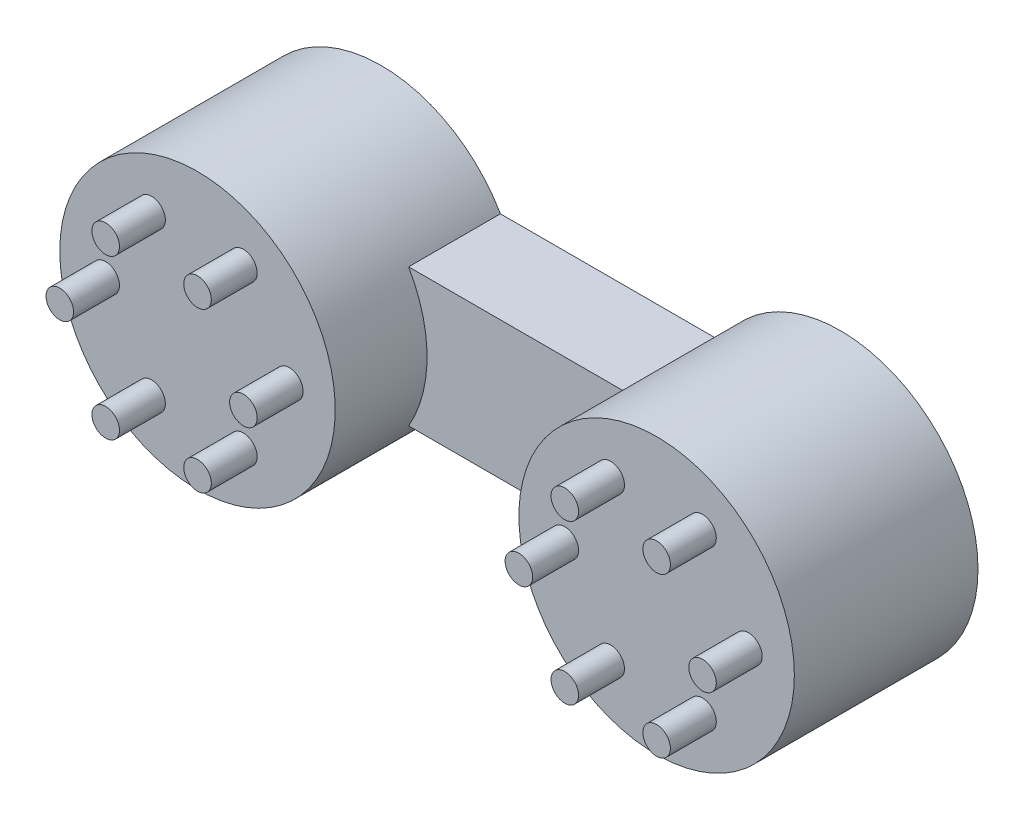
SolidWorks part; units mm, degrees
material "ABS"
ref_plane "Front Plane" through (0, 0, 0) normal (0, 0, 1) x (1, 0, 0)
ref_plane "Top Plane" through (0, 0, 0) normal (0, 1, 0) x (1, 0, 0)
ref_plane "Right Plane" through (0, 0, 0) normal (1, 0, 0) x (0, 0, -1)
sketch "Sketch1" plane through (0, 0, 0) normal (0, 0, 1) x (1, 0, 0)
  line L0 (0, 36.4973) -> (0, -44.5187) construction
  circle A0 centre (25, 0) radius 15
  circle A1 centre (-25, 0) radius 15
  dimension "D2" = 30
  dimension "D1" = 25
extrude "Boss-Extrude1" add sketch "Sketch1" along normal blind 20
sketch "Sketch2" plane through (0, 0, 20) normal (0, 0, 1) x (1, 0, 0)
  line L0 (0, 24.9836) -> (0, -19.9613) construction
  circle A0 centre (35, 0) radius 1.5
  circle A1 centre (30, -8.6603) radius 1.5
  circle A2 centre (20, -8.6603) radius 1.5
  circle A3 centre (15, 0) radius 1.5
  circle A4 centre (20, 8.6603) radius 1.5
  circle A5 centre (30, 8.6603) radius 1.5
  circle A6 centre (25, 0) radius 15 construction
  circle A8 centre (-15, 0) radius 1.5
  circle A9 centre (-20, -8.6603) radius 1.5
  circle A10 centre (-30, -8.6603) radius 1.5
  circle A11 centre (-35, 0) radius 1.5
  circle A12 centre (-30, 8.6603) radius 1.5
  circle A13 centre (-20, 8.6603) radius 1.5
  point P15 (25, 0)
  dimension "D1" = 3
  dimension "D3" = 10
  dimension "D2" = 6
extrude "Boss-Extrude2" add sketch "Sketch2" along normal blind 5
sketch "Sketch3" plane through (0, 0, 0) normal (0, 0, 1) x (1, 0, 0)
  line L1 (-25, 7.5) -> (25, 7.5)
  line L2 (-25, 7.5) -> (-25, -7.5)
  line L3 (-25, -7.5) -> (25, -7.5)
  line L4 (25, 7.5) -> (25, -7.5)
  line L5 (-25, 7.5) -> (25, -7.5) construction
  line L6 (-25, -7.5) -> (25, 7.5) construction
  point P0 (0, 0)
  dimension "D1" = 15
  dimension "D2" = 50
extrude "Boss-Extrude3" add sketch "Sketch3" along normal blind 10
